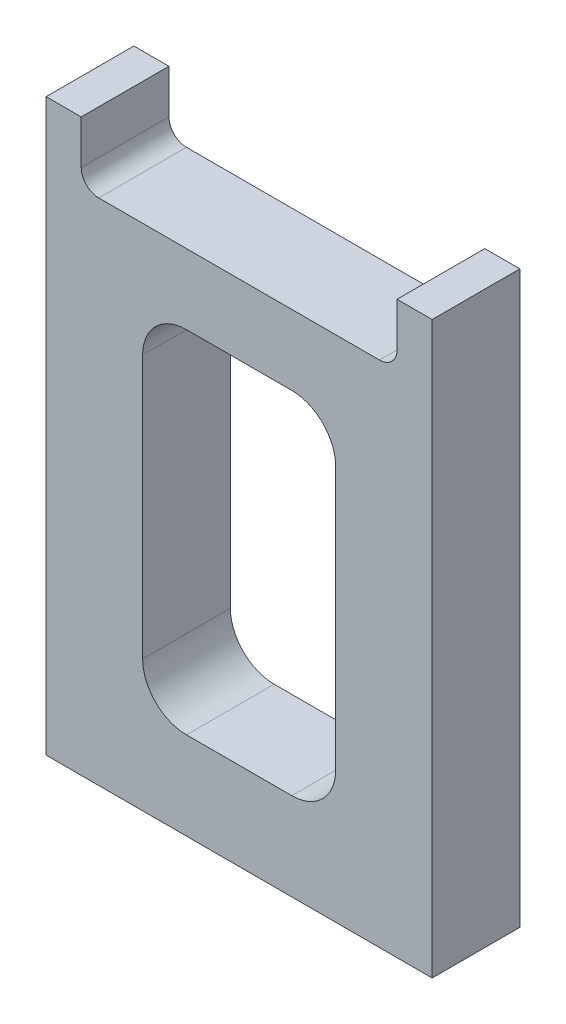
SolidWorks part; units mm, degrees
material "1060 Alloy"
ref_plane "Front Plane" through (0, 0, 0) normal (0, 0, 1) x (1, 0, 0)
ref_plane "Top Plane" through (0, 0, 0) normal (0, 1, 0) x (1, 0, 0)
ref_plane "Right Plane" through (0, 0, 0) normal (1, 0, 0) x (0, 0, -1)
sketch "Sketch1" plane through (0, 0, 0) normal (0, 0, 1) x (1, 0, 0)
  line L0 (-22, 0) -> (22, 0)
  line L1 (22, 0) -> (22, 65)
  line L2 (22, 65) -> (18, 65)
  line L3 (18, 65) -> (18, 58)
  line L4 (18, 58) -> (-18, 58)
  line L5 (0, 0) -> (0, 58) construction
  line L6 (-18, 65) -> (-18, 58)
  line L7 (-22, 65) -> (-18, 65)
  line L8 (-22, 0) -> (-22, 65)
  dimension "D1" = 22
  dimension "D2" = 4
  dimension "D3" = 58
  dimension "D4" = 65
extrude "Boss-Extrude1" add sketch "Sketch1" along normal blind 10
sketch "Sketch2" plane through (0, 0, 0) normal (0, -1, 0) x (1, 0, 0)
  line L0 (-22, 5) -> (22, 5) construction
  line L1 (-22, 10) -> (-22, 0) construction
  line L2 (22, 10) -> (22, 0) construction
  line L3 (0, 5) -> (0, 10) construction
  line L4 (-22, 10) -> (22, 10) construction
  circle A0 centre (15, 5) radius 2
  circle A1 centre (-15, 5) radius 2
  dimension "D1" = 4
  dimension "D2" = 15
extrude "Cut-Extrude1" cut sketch "Sketch2" against normal blind 10
fillet "Fillet1" radius 2 2 edges at (18, 58, 5) (-18, 58, 5)
sketch "Sketch3" plane through (0, 0, 0) normal (0, 0, -1) x (-1, 0, 0)
  line L0 (0, 58) -> (0, 0) construction
  line L1 (-16, 58) -> (16, 58) construction
  line L2 (-22, 30) -> (22, 30) construction
  line L3 (-22, 0) -> (-22, 65) construction
  line L4 (22, 65) -> (22, 0) construction
  line L5 (22, 0) -> (-22, 0) construction
  line L6 (0, 50) -> (0, 10) construction
  line L7 (-11, 50) -> (11, 50)
  line L8 (-11, 50) -> (-11, 10)
  line L9 (-11, 10) -> (11, 10)
  line L10 (11, 50) -> (11, 10)
  line L11 (-11, 30) -> (11, 30) construction
  dimension "D1" = 30
  dimension "D2" = 22
  dimension "D3" = 40
extrude "Cut-Extrude2" cut sketch "Sketch3" against normal through all
fillet "Fillet2" radius 5 4 edges at (11, 10, 5) (-11, 50, 5) (-11, 10, 5) (11, 50, 5)
